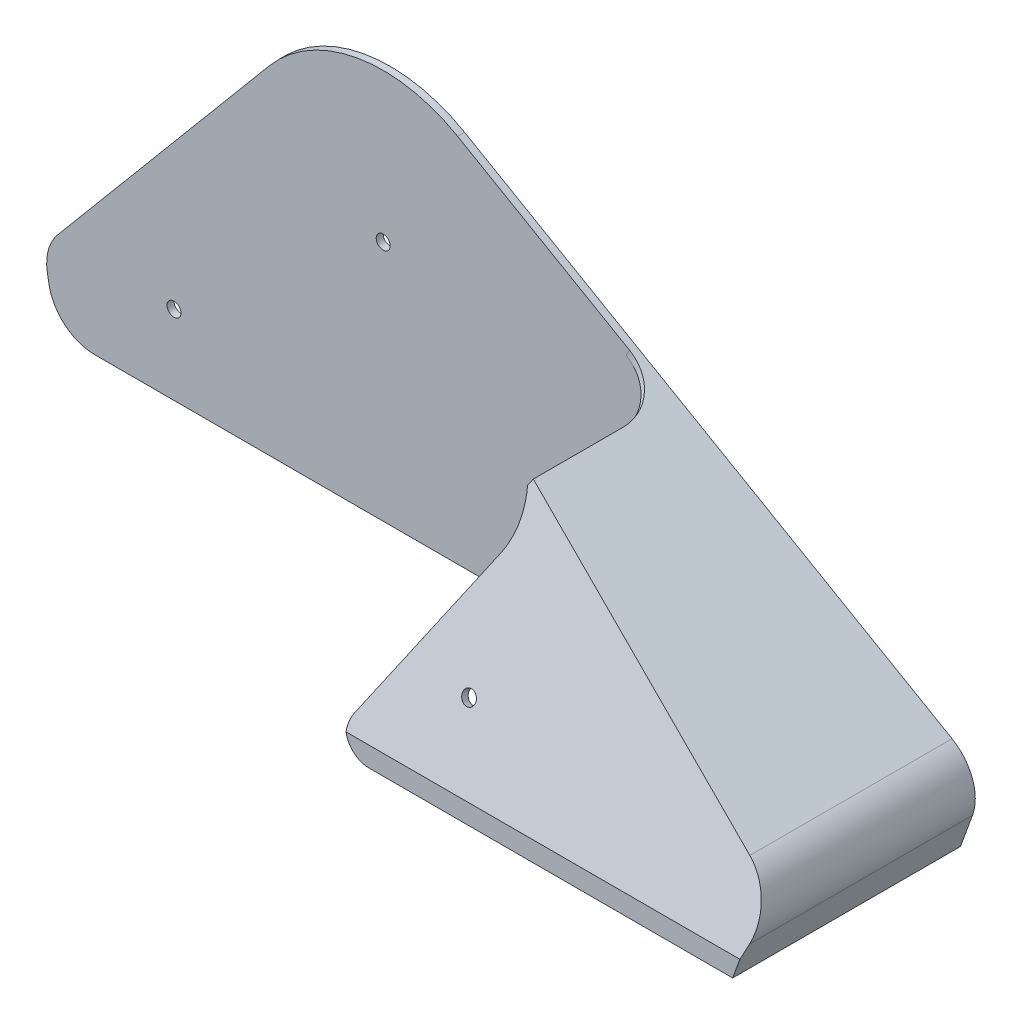
SolidWorks part; units mm, degrees
material "ABS"
ref_plane "前视基准面" through (0, 0, 0) normal (0, 0, 1) x (1, 0, 0)
ref_plane "上视基准面" through (0, 0, 0) normal (0, 1, 0) x (1, 0, 0)
ref_plane "右视基准面" through (0, 0, 0) normal (1, 0, 0) x (0, 0, -1)
other "Configuration Table"
sketch "草图1" plane through (0, 0, 0) normal (0, 0, 1) x (1, 0, 0)
  line L0 (-186.419, -172.0768) -> (-234.498, -229.3751)
  line L1 (-147.8047, -165.2681) -> (-36.7681, -229.3751)
  line L2 (-36.7681, -229.3751) -> (-41.9753, -243.6818)
  line L3 (-41.9753, -243.6818) -> (-231.9753, -243.6818)
  line L4 (-231.9753, -243.6818) -> (-234.498, -229.3751)
  line L5 (-163.0547, -191.6818) -> (-163.0547, -243.6818) construction
  line L6 (-36.7681, -229.3751) -> (-234.498, -229.3751) construction
  arc A0 (-147.8047, -165.2681) -> (-186.419, -172.0768) centre (-163.0547, -191.6818) ccw
  circle A1 centre (-163.0547, -191.6818) radius 1.5
  dimension "D1" = 61
  dimension "D8" = 3
  dimension "D2" = 40
  dimension "D3" = 60
  dimension "D4" = 190
  dimension "D5" = 110
  dimension "D6" = 52
  dimension "D7" = 100
extrude "凸台-拉伸1" add sketch "草图1" along normal blind 46
sketch "草图5" plane through (0, -329.0528, 0) normal (-1, 0, 0) x (0, 1, 0)
  line L0 (135.3709, 0) -> (135.3709, -29) construction
  line L2 (85.3709, -46) -> (85.3709, 0) construction
  line L3 (99.6777, 0) -> (163.7847, 0) construction
  dimension "D1" = 29
  dimension "D2" = 50
sketch "草图9" plane through (0, 0, 46) normal (0, 0, 1) x (1, 0, 0)
  line L0 (-232.6806, -239.6818) -> (-40.5194, -239.6818)
  line L1 (-234.498, -229.3751) -> (-231.9753, -243.6818) construction
  line L2 (-41.9753, -243.6818) -> (-36.7681, -229.3751) construction
  line L3 (-231.9753, -243.6818) -> (-41.9753, -243.6818) construction
  arc A0 (-147.8047, -165.2681) -> (-186.419, -172.0768) centre (-163.0547, -191.6818) ccw construction
  dimension "D1" = 48
ref_plane "基准面1" through (0, -13.8445, -37.4616) normal (0, 0.3467, 0.938) x (1, 0, 0)
sketch "草图6" plane through (0, -13.8445, -37.4616) normal (0, 0.3467, 0.938) x (1, 0, 0)
  line L1 (-256.6496, -137.425) -> (-12.55, -137.425)
  line L2 (-256.6496, -137.425) -> (-256.6496, -270.7714)
  line L3 (-256.6496, -270.7714) -> (-12.55, -270.7714)
  line L4 (-12.55, -137.425) -> (-12.55, -270.7714)
  line L5 (-256.6496, -137.425) -> (-12.55, -270.7714) construction
  line L6 (-256.6496, -270.7714) -> (-12.55, -137.425) construction
  point P4 (-134.5998, -204.0982)
extrude "切除-拉伸3" cut sketch "草图6" along normal through all
shell "抽壳1" thickness 1.5
sketch "草图2" plane through (0, 0, -1.5) normal (0, 0, -1) x (-1, 0, 0)
  line L1 (103.6912, -202.8613) -> (127.2589, -243.6818)
  line L16 (147.0547, -163.969) -> (34.928, -228.7054)
  line L17 (34.928, -228.7054) -> (40.379, -243.6818)
  line L23 (40.379, -243.6818) -> (233.4984, -243.6818)
  line L24 (233.4984, -243.6818) -> (236.0966, -228.9467)
  line L25 (236.0966, -228.9467) -> (187.5681, -171.1126)
  line L26 (147.0547, -163.969) -> (102.8874, -189.469)
  line L28 (127.2589, -243.6818) -> (233.4984, -243.6818)
  line L29 (233.4984, -243.6818) -> (236.0966, -228.9467)
  line L30 (236.0966, -228.9467) -> (187.5681, -171.1126)
  arc A0 (103.6912, -202.8613) -> (102.8874, -189.469) centre (116.6816, -195.3613) cw
  arc A3 (187.5681, -171.1126) -> (147.0547, -163.969) centre (163.0547, -191.6818) ccw
  arc A5 (187.5681, -171.1126) -> (147.0547, -163.969) centre (163.0547, -191.6818) ccw
  dimension "D4" = 15
  dimension "D2" = 60
  dimension "D3" = 57
  dimension "D1" = 0
  dimension "D5" = 6
extrude "切除-拉伸2" cut sketch "草图2" against normal through all from surface at -1.5 starting at face at (-146.7799, -212.7386, 0)
fillet "圆角2" radius 10 2 edges at (-34.928, -228.7054, 21.0213) (-36.7681, -229.3751, 21.0955)
fillet "圆角3" radius 10 2 edges at (-233.4984, -243.6818, -0.75) (-236.0966, -228.9467, -0.75)
fillet "圆角4" radius 5 1 edges at (-127.2589, -243.6818, 46.75)
sketch "草图7" plane through (-107.7643, -186.6533, 0) normal (0.5, 0.866, 0) x (0.866, -0.5, 0)
  line L1 (7.3436, -34.8107) -> (7.3436, 0)
  line L2 (7.3436, 0) -> (5.6314, 0)
  line L3 (5.6314, 0) -> (5.6314, -34.8107)
  line L4 (5.6314, -34.8107) -> (7.3436, -34.8107)
  line L7 (5.6314, 0) -> (-45.3686, 0) construction
  line L8 (5.6314, -29.0422) -> (5.6314, 0) construction
  line L9 (7.3436, -28.2395) -> (7.3436, 0) construction
extrude "切除-拉伸4" cut sketch "草图7" against normal blind 5 contours L1 L2 L3 L4
fillet "圆角5" radius 10 1 edges at (-101.7796, -190.9746, 0)
sketch "草图10" plane through (0, 0, -1.5) normal (0, 0, -1) x (-1, 0, 0)
  line L0 (63.0547, -226.6818) -> (208.0547, -226.6818) construction
  circle A0 centre (163.0547, -191.6818) radius 1.5 construction
  circle A1 centre (208.0547, -226.6818) radius 1.5
  circle A2 centre (63.0547, -226.6818) radius 1.5
  dimension "D1" = 35
  dimension "D2" = 45
  dimension "D4" = 3
  dimension "D3" = 145
extrude "切除-拉伸5" cut sketch "草图10" against normal blind 2
sketch "草图11" plane through (0, -13.3245, -36.0546) normal (0, 0.3467, 0.938) x (1, 0, 0)
  line L0 (-232.6806, -240.7662) -> (-40.5194, -240.7662) construction
  circle A0 centre (-102.379, -225.7662) radius 1.5
  dimension "D1" = 3
  dimension "D2" = 15
  dimension "D3" = 62
extrude "切除-拉伸6" cut sketch "草图11" against normal blind 2
